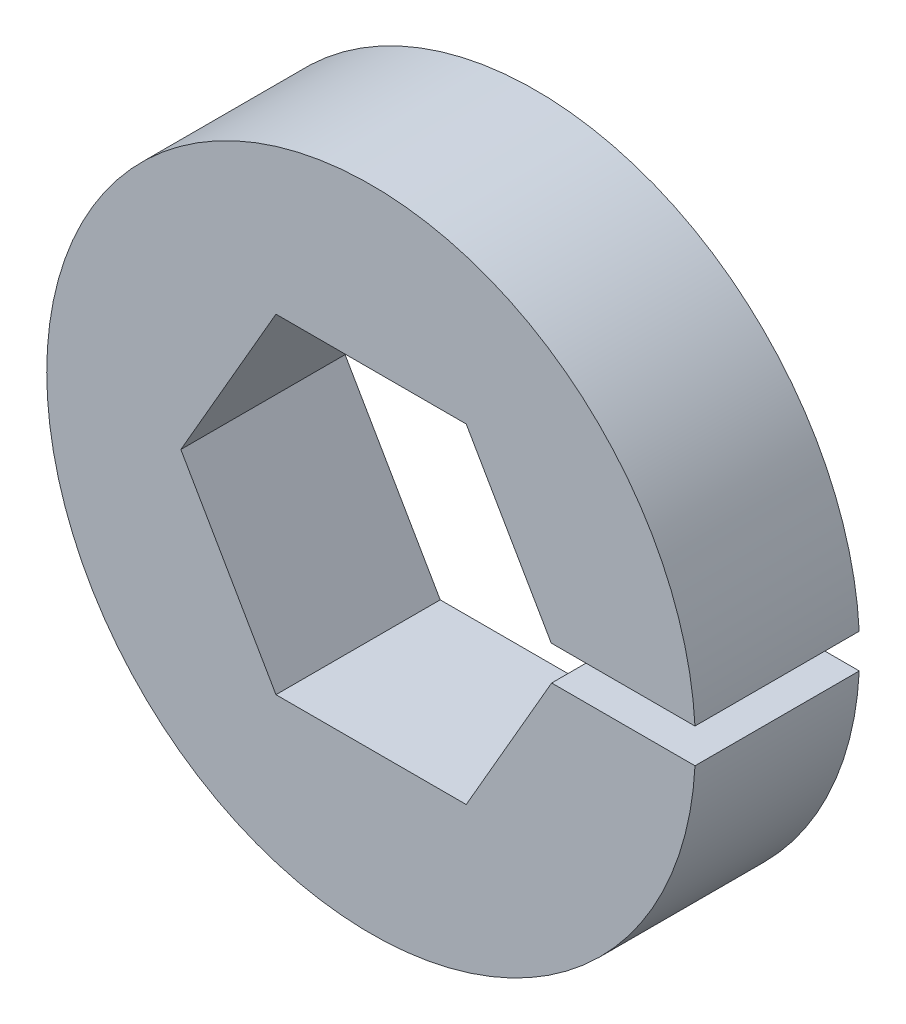
SolidWorks part; units mm, degrees
ref_plane "Front Plane" through (0, 0, 0) normal (0, 0, 1) x (1, 0, 0)
ref_plane "Top Plane" through (0, 0, 0) normal (0, 1, 0) x (1, 0, 0)
ref_plane "Right Plane" through (0, 0, 0) normal (1, 0, 0) x (0, 0, -1)
sketch "Sketch1" plane through (0, 0, 0) normal (0, 0, 1) x (1, 0, 0)
  line L1 (7.3323, 0) -> (3.6662, 6.35)
  line L2 (3.6662, 6.35) -> (-3.6662, 6.35)
  line L3 (-3.6662, 6.35) -> (-7.3323, 0)
  line L4 (-7.3323, 0) -> (-3.6662, -6.35)
  line L5 (-3.6662, -6.35) -> (3.6662, -6.35)
  line L6 (3.6662, -6.35) -> (7.3323, 0)
  circle A0 centre (0, 0) radius 6.35 construction
  circle A1 centre (0, 0) radius 12.5
  dimension "D2" = 25
  dimension "D1" = 12.7
extrude "Boss-Extrude1" add sketch "Sketch1" along normal blind 6.33
sketch "Sketch2" plane through (0, 0, 6.33) normal (0, 0, 1) x (1, 0, 0)
  line L1 (6.1962, 0.6763) -> (14.6574, 0.6763)
  line L2 (6.1962, 0.6763) -> (6.1962, -0.6477)
  line L3 (6.1962, -0.6477) -> (14.6574, -0.6477)
  line L4 (14.6574, 0.6763) -> (14.6574, -0.6477)
extrude "Cut-Extrude1" cut sketch "Sketch2" against normal through all
